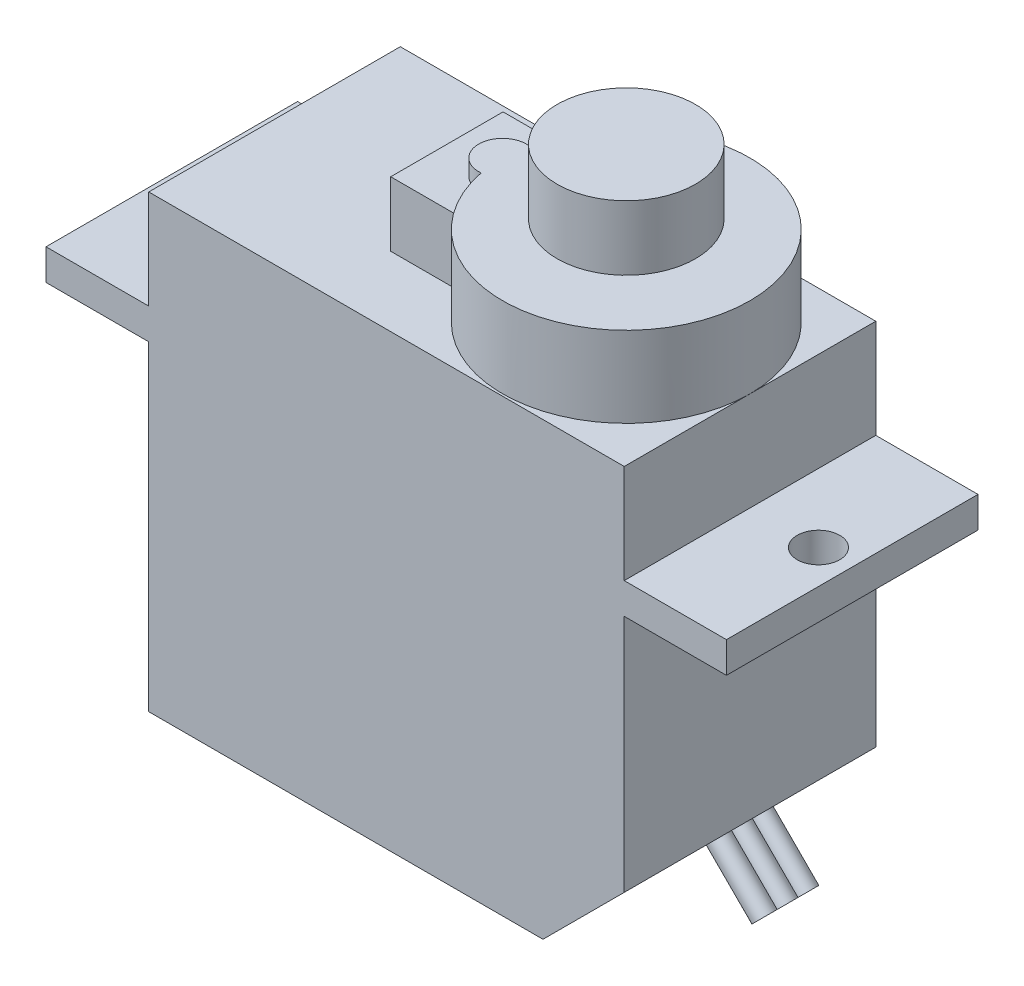
SolidWorks part; units mm, degrees
ref_plane "Front Plane" through (0, 0, 0) normal (0, 0, 1) x (1, 0, 0)
ref_plane "Top Plane" through (0, 0, 0) normal (0, 1, 0) x (1, 0, 0)
ref_plane "Right Plane" through (0, 0, 0) normal (1, 0, 0) x (0, 0, -1)
sketch "Sketch1" plane through (0, 0, 0) normal (0, 0, 1) x (1, 0, 0)
  line L0 (19.12, 0) -> (23.06, 3.94)
  line L1 (0, 0) -> (19.12, 0)
  line L2 (0, 0) -> (0, 21.83)
  line L3 (0, 21.83) -> (23.06, 21.83)
  line L4 (23.06, 3.94) -> (23.06, 21.83)
  point P3 (23.06, 0)
  point P5 (0, 0)
  dimension "D1" = 3.94
  dimension "D2" = 45
extrude "Boss-Extrude1" add sketch "Sketch1" against normal blind 12.2
sketch "Sketch4" plane through (0, 0, 0) normal (0, 0, 1) x (1, 0, 0)
  line L1 (-4.9829, 15.5353) -> (28.0171, 15.5353)
  line L2 (-4.9829, 15.5353) -> (-4.9829, 17.0353)
  line L3 (-4.9829, 17.0353) -> (28.0171, 17.0353)
  line L4 (28.0171, 15.5353) -> (28.0171, 17.0353)
extrude "Boss-Extrude2" add sketch "Sketch4" against normal blind 12.2 separate body
ref_plane "Plane1" through (0, 17, 0) normal (0, 1, 0) x (1, 0, 0)
sketch "Sketch6" plane through (0, 17, 0) normal (0, 1, 0) x (1, 0, 0)
  circle A0 centre (-3.31, 6.1) radius 1.03
extrude "Cut-Extrude1" cut sketch "Sketch6" against normal through all both and the other way through all
sketch "Sketch7" plane through (0, 17, 0) normal (0, 1, 0) x (1, 0, 0)
  circle A0 centre (26.38, 6.1) radius 1.03
extrude "Cut-Extrude2" cut sketch "Sketch7" against normal through all both and the other way through all
sketch "Sketch9" plane through (0, 17, 0) normal (0, 1, 0) x (1, 0, 0)
  circle A0 centre (17.06, 6.1) radius 6
extrude "Boss-Extrude3" add sketch "Sketch9" along normal blind 8.74
sketch "Sketch11" plane through (0, 17, 0) normal (0, 1, 0) x (1, 0, 0)
  circle A0 centre (11.06, 6.1) radius 1.16
  circle A1 centre (17.06, 6.1) radius 6 construction
  circle A2 centre (17.06, 6.1) radius 6 construction
extrude "Boss-Extrude4" add sketch "Sketch11" along normal blind 8.74
sketch "Sketch13" plane through (0, 17, 0) normal (0, 1, 0) x (1, 0, 0)
  line L1 (13.76, 3.375) -> (8.36, 3.375)
  line L2 (13.76, 3.375) -> (13.76, 8.825)
  line L3 (13.76, 8.825) -> (8.36, 8.825)
  line L4 (8.36, 3.375) -> (8.36, 8.825)
  line L5 (13.76, 3.375) -> (8.36, 8.825) construction
  line L6 (13.76, 8.825) -> (8.36, 3.375) construction
  point P0 (11.06, 6.1)
extrude "Boss-Extrude5" add sketch "Sketch13" along normal blind 7.96
sketch "Sketch14" plane through (0, 17, 0) normal (0, 1, 0) x (1, 0, 0)
  circle A0 centre (17.06, 6.1) radius 2.345
extrude "Boss-Extrude6" add sketch "Sketch14" along normal blind 11.51
ref_plane "Plane2" through (0, 28.51, 0) normal (0, 1, 0) x (1, 0, 0)
sketch "Sketch15" plane through (0, 28.51, 0) normal (0, 1, 0) x (1, 0, 0)
  circle A0 centre (17.06, 6.1) radius 0.635
extrude "Cut-Extrude3" cut sketch "Sketch15" against normal blind 3.13
sketch "Sketch17" plane through (0, 28.51, 0) normal (0, 1, 0) x (1, 0, 0)
  circle A0 centre (17.06, 6.1) radius 3.355
extrude "Boss-Extrude7" add sketch "Sketch17" against normal blind 3.13 from offset 0.8
sketch "Sketch18" plane through (9.56, -9.56, 0) normal (0.7071, -0.7071, 0) x (0, 0, -1)
  line L0 (6.1, 19.0919) -> (6.1, 13.5199) construction
  line L1 (12.2, 19.0919) -> (0, 19.0919) construction
  line L2 (12.2, 13.5199) -> (0, 13.5199) construction
  circle A1 centre (5.09, 18.387) radius 0.5
  circle A2 centre (6.1, 18.387) radius 0.5
  circle A3 centre (7.11, 18.387) radius 0.5
extrude "Boss-Extrude8" add sketch "Sketch18" along normal blind 3.13
